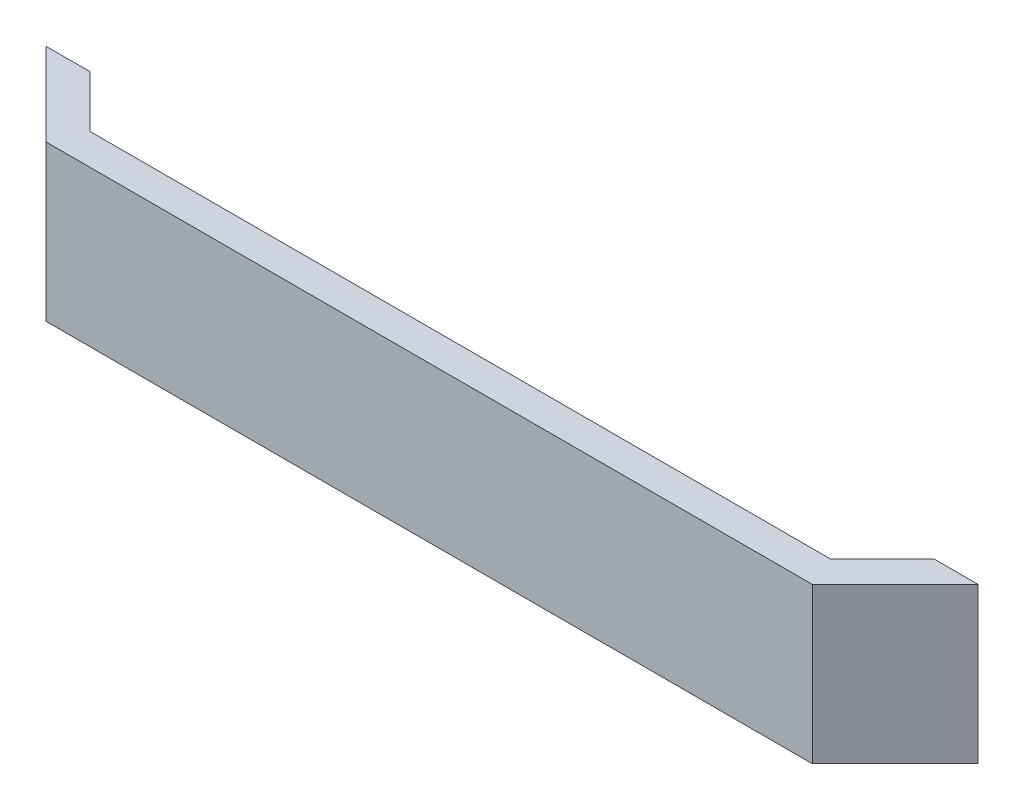
SolidWorks part; units mm, degrees
ref_plane "Alzado" through (0, 0, 0) normal (0, 0, 1) x (1, 0, 0)
ref_plane "Planta" through (0, 0, 0) normal (0, 1, 0) x (1, 0, 0)
ref_plane "Vista lateral" through (0, 0, 0) normal (1, 0, 0) x (0, 0, -1)
sketch "Croquis1" plane through (0, 0, 0) normal (0, 1, 0) x (1, 0, 0)
  line L0 (-37, 0) -> (37, 0)
  line L1 (-37, 0) -> (-45, 8)
  line L2 (37, 0) -> (45, 8)
  line L3 (-35.7574, 3) -> (-40.7574, 8)
  line L4 (-35.7574, 3) -> (35.7574, 3)
  line L5 (35.7574, 3) -> (40.7574, 8)
  line L6 (-45, 8) -> (-40.7574, 8)
  line L7 (-35.7574, 3) -> (-42.8787, 10.1213) construction
  line L8 (40.7574, 8) -> (45, 8)
  line L9 (35.7574, 3) -> (42.8787, 10.1213) construction
  point P4 (0, 0)
  dimension "D1" = 74
  dimension "D2" = 8
  dimension "D3" = 45
  dimension "D4" = 8
  dimension "D5" = 45
  dimension "D6" = 3
extrude "Saliente-Extruir1" add sketch "Croquis1" along normal blind 15
